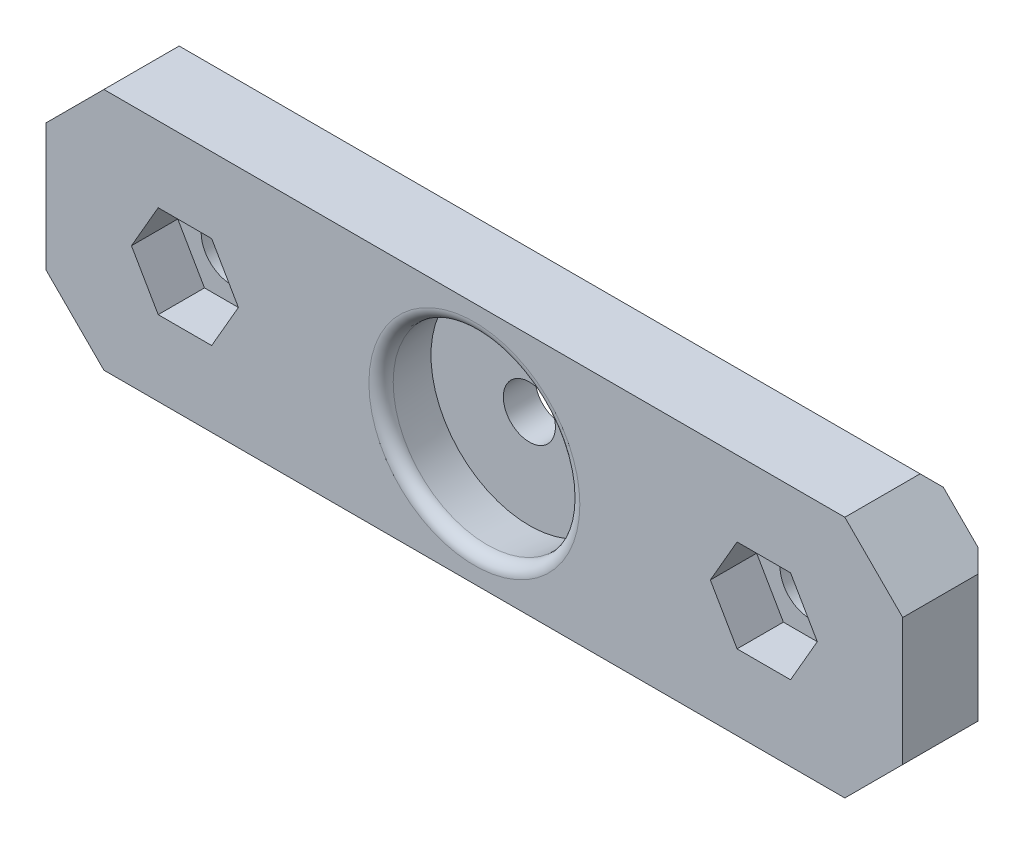
SolidWorks part; units mm, degrees
ref_plane "Front Plane" through (0, 0, 0) normal (0, 0, 1) x (1, 0, 0)
ref_plane "Top Plane" through (0, 0, 0) normal (0, 1, 0) x (1, 0, 0)
ref_plane "Right Plane" through (0, 0, 0) normal (1, 0, 0) x (0, 0, -1)
sketch "Sketch1" plane through (0, 0, 0) normal (0, 0, 1) x (1, 0, 0)
  line L1 (-37, -10.5) -> (37, -10.5)
  line L2 (-37, -10.5) -> (-37, 10.5)
  line L3 (-37, 10.5) -> (37, 10.5)
  line L4 (37, -10.5) -> (37, 10.5)
  line L5 (-37, -10.5) -> (37, 10.5) construction
  line L6 (-37, 10.5) -> (37, -10.5) construction
  point P0 (0, 0)
  dimension "D1" = 74
  dimension "D2" = 21
extrude "Boss-Extrude1" add sketch "Sketch1" along normal blind 7.5
sketch "Sketch2" plane through (0, 0, 7.5) normal (0, 0, 1) x (1, 0, 0)
  line L0 (-36.805, 0) -> (36.9536, 0) construction
  circle A0 centre (0, 0) radius 8
  dimension "D1" = 16
extrude "Cut-Extrude1" cut sketch "Sketch2" against normal blind 4.75 draft 6 draft outward yes
sketch "Sketch4" plane through (0, 0, 0) normal (0, 0, -1) x (-1, 0, 0)
  line L0 (-37, 0) -> (-25, 0) construction
  line L1 (-37, -10.5) -> (-37, 10.5) construction
  line L2 (0, 10.5) -> (0, -11.0022) construction
  line L3 (-37, 10.5) -> (37, 10.5) construction
  line L4 (37, 0) -> (25, 0) construction
  circle A0 centre (-25, 0) radius 2.6
  circle A1 centre (25, 0) radius 2.6
  dimension "D2" = 5.2
  dimension "D3" = 5.2
  dimension "D1" = 25
extrude "Cut-Extrude4" cut sketch "Sketch4" against normal through all
chamfer "Chamfer3" distance 5 angle 45 4 edges at (-37, 10.5, 3.75) (-37, -10.5, 3.75) (37, 10.5, 3.75) (37, -10.5, 3.75)
sketch "Sketch5" plane through (0, 0, 7.5) normal (0, 0, 1) x (1, 0, 0)
  line L0 (37, 0) -> (25, 0) construction
  line L1 (37, -5.5) -> (37, 5.5) construction
  line L2 (-37, 0) -> (-25, 0) construction
  line L3 (-37, 5.5) -> (-37, -5.5) construction
  line L5 (22.6906, -4) -> (27.3094, -4)
  line L6 (27.3094, -4) -> (29.6188, 0)
  line L7 (29.6188, 0) -> (27.3094, 4)
  line L8 (27.3094, 4) -> (22.6906, 4)
  line L9 (22.6906, 4) -> (20.3812, 0)
  line L10 (20.3812, 0) -> (22.6906, -4)
  line L11 (-27.3094, -4) -> (-22.6906, -4)
  line L12 (-22.6906, -4) -> (-20.3812, 0)
  line L13 (-20.3812, 0) -> (-22.6906, 4)
  line L14 (-22.6906, 4) -> (-27.3094, 4)
  line L15 (-27.3094, 4) -> (-29.6188, 0)
  line L16 (-29.6188, 0) -> (-27.3094, -4)
  circle A0 centre (25, 0) radius 4 construction
  circle A1 centre (-25, 0) radius 4 construction
  dimension "D1" = 8
  dimension "D2" = 8
extrude "Cut-Extrude6" cut sketch "Sketch5" against normal blind 4
sketch "Sketch11" plane through (0, 0, 7.5) normal (0, 0, 1) x (1, 0, 0)
  circle A0 centre (0, 0) radius 2.25
  dimension "D1" = 4.5
extrude "Cut-Extrude10" cut sketch "Sketch11" against normal through all
fillet "Fillet4" radius 1 2 edges at (-27.6, 0, 0) (22.4, 0, 0)
fillet "Fillet5" radius 1 1 edges at (8, 0, 7.5)
chamfer "Chamfer5" distance 1 angle 45 4 edges at (-37, 0, 0) (37, 0, 0) (0, 10.5, 0) (0, -10.5, 0)
